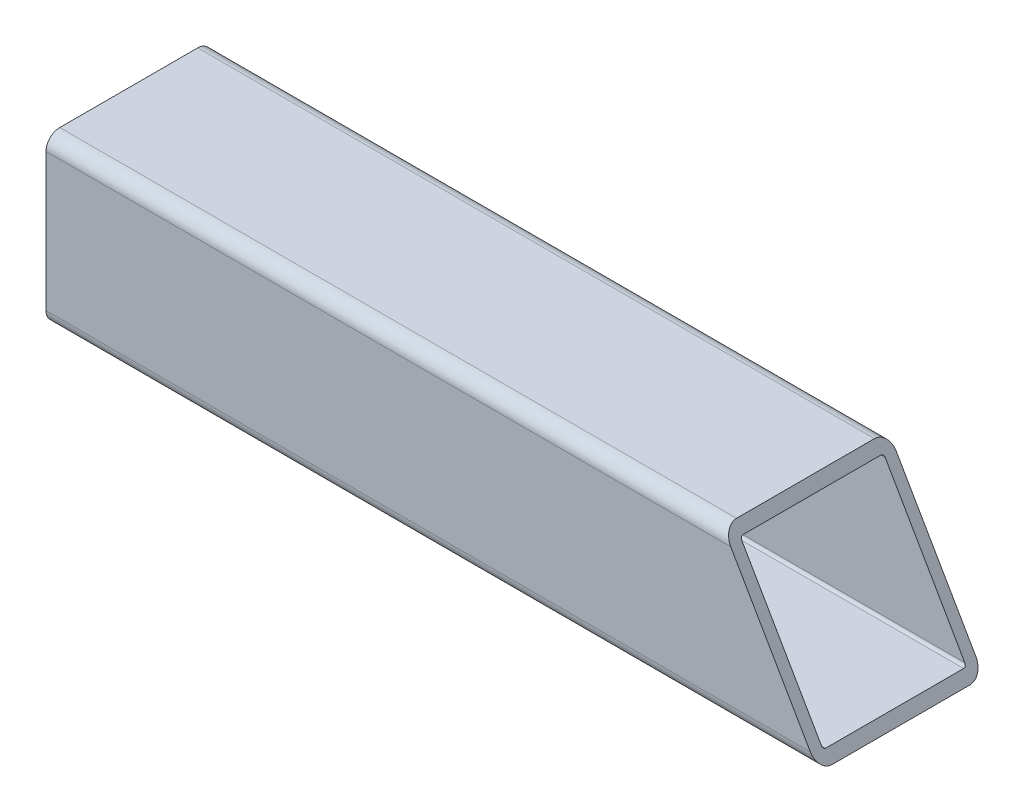
SolidWorks part; units mm, degrees
ref_plane "Front Plane" through (0, 0, 0) normal (0, 0, 1) x (1, 0, 0)
ref_plane "Top Plane" through (0, 0, 0) normal (0, 1, 0) x (1, 0, 0)
ref_plane "Right Plane" through (0, 0, 0) normal (1, 0, 0) x (0, 0, -1)
sketch "Sketch1" plane through (0, 0, 0) normal (1, 0, 0) x (0, 0, -1)
  line L1 (-15.875, 19.05) -> (15.875, 19.05)
  line L2 (-19.05, 15.875) -> (-19.05, -15.875)
  line L3 (-15.875, -19.05) -> (15.875, -19.05)
  line L4 (19.05, 15.875) -> (19.05, -15.875)
  line L5 (-19.05, 19.05) -> (19.05, -19.05) construction
  line L6 (-19.05, -19.05) -> (19.05, 19.05) construction
  arc A0 (-19.05, -15.875) -> (-15.875, -19.05) centre (-15.875, -15.875) ccw
  arc A1 (15.875, -19.05) -> (19.05, -15.875) centre (15.875, -15.875) ccw
  arc A2 (19.05, 15.875) -> (15.875, 19.05) centre (15.875, 15.875) ccw
  arc A3 (-15.875, 19.05) -> (-19.05, 15.875) centre (-15.875, 15.875) ccw
  point P0 (0, 0)
  dimension "D3" = 3.175
  dimension "D1" = 38.1
  dimension "D2" = 38.1
extrude "Extrude-Thin1" add sketch "Sketch1" along normal mid plane 177.8 thin
sketch "Sketch2" plane through (0, 0, 19.05) normal (0, 0, 1) x (1, 0, 0)
  line L0 (88.9, -19.05) -> (66.903, 19.05)
  line L3 (88.9, 19.05) -> (-88.9, 19.05) construction
  line L4 (88.9, 15.875) -> (88.9, -15.875) construction
  dimension "D1" = 30
extrude "Cut-Extrude1" cut sketch "Sketch2" against normal through all and the other way through all flip side to cut
